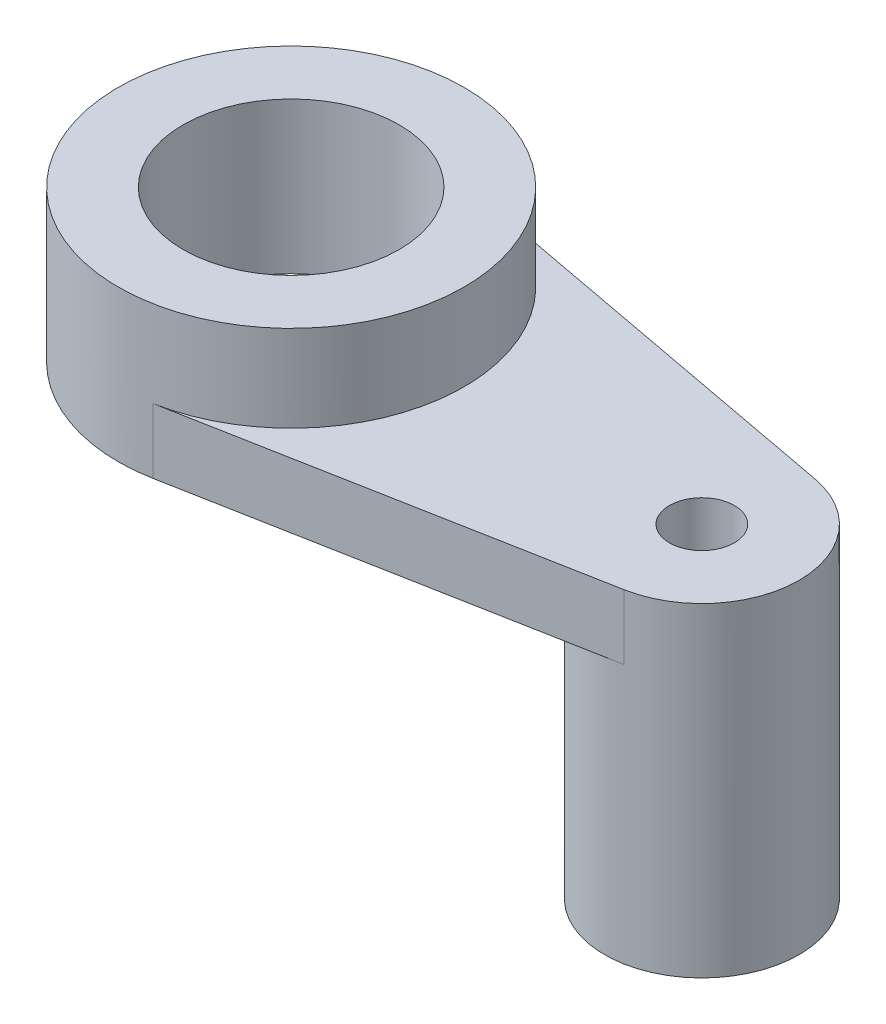
SolidWorks part; units mm, degrees
ref_plane "Front Plane" through (0, 0, 0) normal (0, 0, 1) x (1, 0, 0)
ref_plane "Top Plane" through (0, 0, 0) normal (0, 1, 0) x (1, 0, 0)
ref_plane "Right Plane" through (0, 0, 0) normal (1, 0, 0) x (0, 0, -1)
sketch "Sketch1" plane through (0, 0, 0) normal (0, 1, 0) x (1, 0, 0)
  line L1 (2.9474, 15.7262) -> (39.6579, 8.846)
  line L2 (2.9474, -15.7262) -> (39.6579, -8.846)
  arc A0 (2.9474, -15.7262) -> (2.9474, 15.7262) centre (0, 0) ccw
  arc A1 (39.6579, -8.846) -> (39.6579, 8.846) centre (38, 0) ccw
  dimension "D1" = 32
  dimension "D2" = 18
  dimension "D3" = 38
extrude "Boss-Extrude1" add sketch "Sketch1" along normal blind 6
sketch "Sketch2" plane through (0, 6, 0) normal (0, 1, 0) x (1, 0, 0)
  circle A0 centre (38, 0) radius 3
extrude "Cut-Extrude1" cut sketch "Sketch2" against normal blind 14
sketch "Sketch3" plane through (0, 0, 0) normal (0, -1, 0) x (1, 0, 0)
  circle A0 centre (0, 0) radius 16
  circle A1 centre (0, 0) radius 10
extrude "Boss-Extrude2" add sketch "Sketch3" against normal blind 14
sketch "Sketch4" plane through (0, 0, 0) normal (0, -1, 0) x (1, 0, 0)
  circle A0 centre (38, 0) radius 9
  circle A1 centre (38, 0) radius 3
extrude "Boss-Extrude3" add sketch "Sketch4" along normal blind 24
